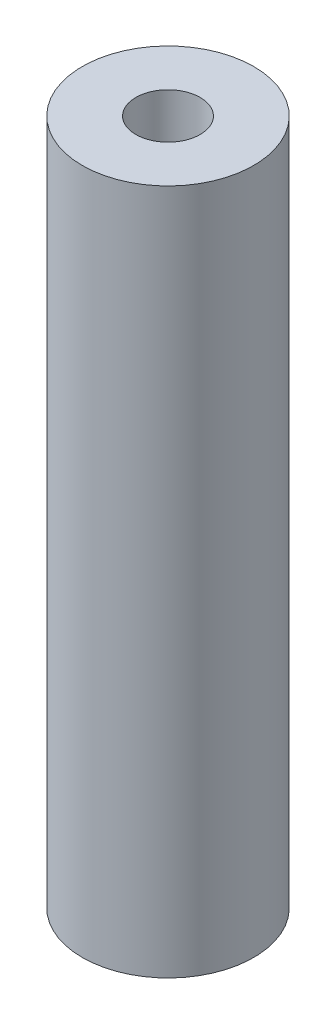
SolidWorks part; units mm, degrees
ref_plane "Front Plane" through (0, 0, 0) normal (0, 0, 1) x (1, 0, 0)
ref_plane "Top Plane" through (0, 0, 0) normal (0, 1, 0) x (1, 0, 0)
ref_plane "Right Plane" through (0, 0, 0) normal (1, 0, 0) x (0, 0, -1)
sketch "Sketch1" plane through (0, 0, 0) normal (0, 1, 0) x (1, 0, 0)
  circle A0 centre (0, 0) radius 4.7625
  circle A1 centre (0, 0) radius 12.7
  dimension "D1" = 9.525
  dimension "D2" = 25.4
extrude "Boss-Extrude1" add sketch "Sketch1" along normal blind 101.6
move or copy body "Body-Move/Copy2" bodies to move or copy 101
move or copy body "Body-Move/Copy1" [suppressed] bodies to move or copy 101
